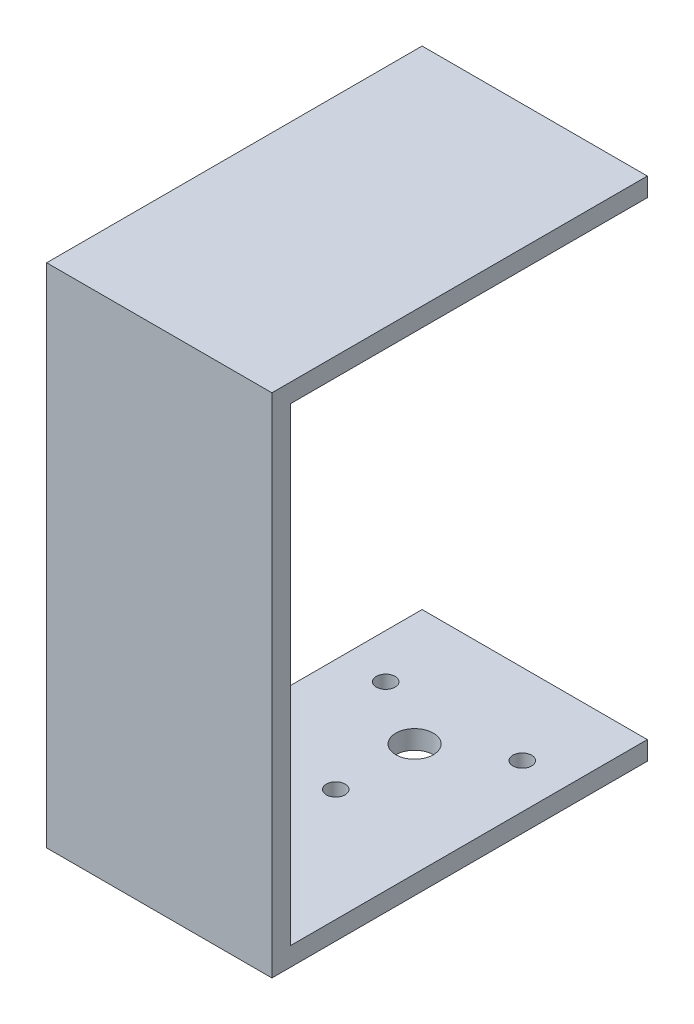
SolidWorks part; units mm, degrees
ref_plane "Front Plane" through (0, 0, 0) normal (0, 0, 1) x (1, 0, 0)
ref_plane "Top Plane" through (0, 0, 0) normal (0, 1, 0) x (1, 0, 0)
ref_plane "Right Plane" through (0, 0, 0) normal (1, 0, 0) x (0, 0, -1)
sketch "Sketch1" plane through (0, 0, 0) normal (0, 1, 0) x (1, 0, 0)
  line L0 (0, 0) -> (-60, 0)
  line L1 (-60, 0) -> (-60, 100)
  line L2 (-60, 100) -> (0, 100)
  line L3 (0, 100) -> (0, 0)
extrude "Boss-Extrude1" add sketch "Sketch1" along normal blind 5
sketch "Sketch2" plane through (0, 5, 0) normal (0, 1, 0) x (1, 0, 0)
  line L0 (0, 0) -> (0, 100) construction
  line L1 (-60, 0) -> (0, 0)
  line L2 (-60, 0) -> (-60, 5)
  line L3 (-60, 5) -> (0, 5)
  line L4 (0, 0) -> (0, 5)
extrude "Boss-Extrude2" add sketch "Sketch2" along normal blind 130
sketch "Sketch3" plane through (0, 0, -5) normal (0, 0, -1) x (-1, 0, 0)
  line L0 (60, 135) -> (60, 5) construction
  line L1 (0, 135) -> (60, 135)
  line L2 (0, 135) -> (0, 130)
  line L3 (0, 130) -> (60, 130)
  line L4 (60, 135) -> (60, 130)
extrude "Boss-Extrude3" add sketch "Sketch3" along normal blind 55
sketch "Sketch9" plane through (0, 0, 0) normal (0, -1, 0) x (-1, 0, 0)
  line L1 (60, 100) -> (0, 100)
  line L2 (60, 100) -> (60, 60)
  line L3 (60, 60) -> (0, 60)
  line L4 (0, 100) -> (0, 60)
extrude "Cut-Extrude1" cut sketch "Sketch9" against normal blind 55
sketch "Sketch11" plane through (0, 0, -60) normal (0, 0, -1) x (-1, 0, 0)
  line L0 (60, 130) -> (60, 135) construction
  line L1 (0, 135) -> (60, 135)
  line L2 (0, 135) -> (0, 130)
  line L3 (0, 130) -> (60, 130)
  line L4 (60, 135) -> (60, 130)
  line L5 (0, 130) -> (60, 130) construction
extrude "Boss-Extrude4" add sketch "Sketch11" along normal blind 40
sketch "Sketch12" plane through (0, 0, -60) normal (0, 0, -1) x (-1, 0, 0)
  line L0 (0, 5) -> (60, 5) construction
  line L1 (0, 5) -> (60, 5)
  line L2 (0, 5) -> (0, 0)
  line L3 (0, 0) -> (60, 0)
  line L4 (60, 5) -> (60, 0)
  line L5 (0, 5) -> (0, 0) construction
extrude "Boss-Extrude5" add sketch "Sketch12" along normal blind 40
sketch "Sketch13" plane through (0, 0, 0) normal (0, -1, 0) x (1, 0, 0)
  line L0 (0, -100) -> (-60, -100) construction
  line L1 (-60, -100) -> (-60, 0) construction
  circle A0 centre (-30, -68) radius 5
  dimension "D1" = 32
  dimension "D3" = 10
  dimension "D2" = 30
extrude "Cut-Extrude2" cut sketch "Sketch13" against normal blind 40
sketch "Sketch14" plane through (0, 0, 0) normal (0, -1, 0) x (1, 0, 0)
  circle A2 centre (-30, -47) radius 2.5
  circle A3 centre (-48.1865, -78.5) radius 2.5
  circle A4 centre (-11.8135, -78.5) radius 2.5
extrude "Cut-Extrude3" cut sketch "Sketch14" against normal blind 40
